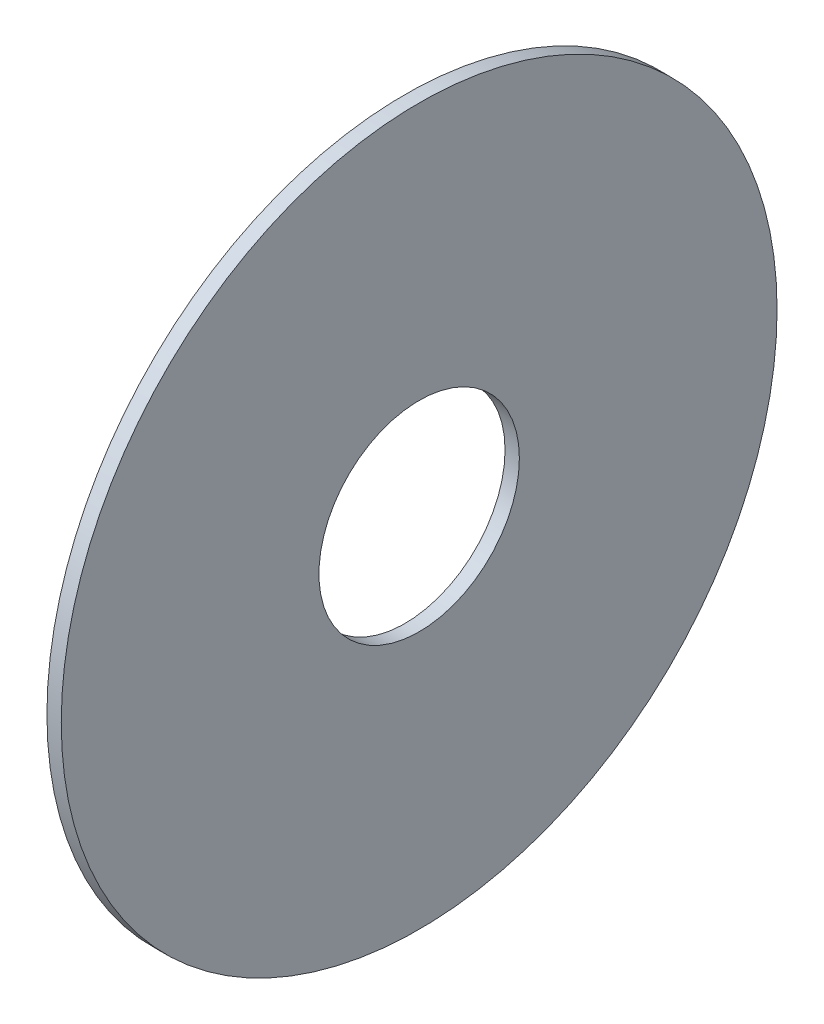
SolidWorks part; units mm, degrees
ref_plane "Front" through (0, 0, 0) normal (0, 0, 1) x (1, 0, 0)
ref_plane "Top" through (0, 0, 0) normal (0, 1, 0) x (1, 0, 0)
ref_plane "Right" through (0, 0, 0) normal (1, 0, 0) x (0, 0, -1)
sketch "Sketch1" plane through (0, 0, 0) normal (1, 0, 0) x (0, 0, -1)
  circle A0 centre (0, 0) radius 5.334
  circle A1 centre (0, 0) radius 19.05
  point P4 (0, 0)
  point P5 (0, 0)
  point P6 (0, 0)
  point P7 (0, 0)
  point P8 (7.3954, 1.4805)
  dimension "D1" = 10.668
  dimension "D2" = 38.1
extrude "Boss-Extrude2" add sketch "Sketch1" along normal blind 0.762
